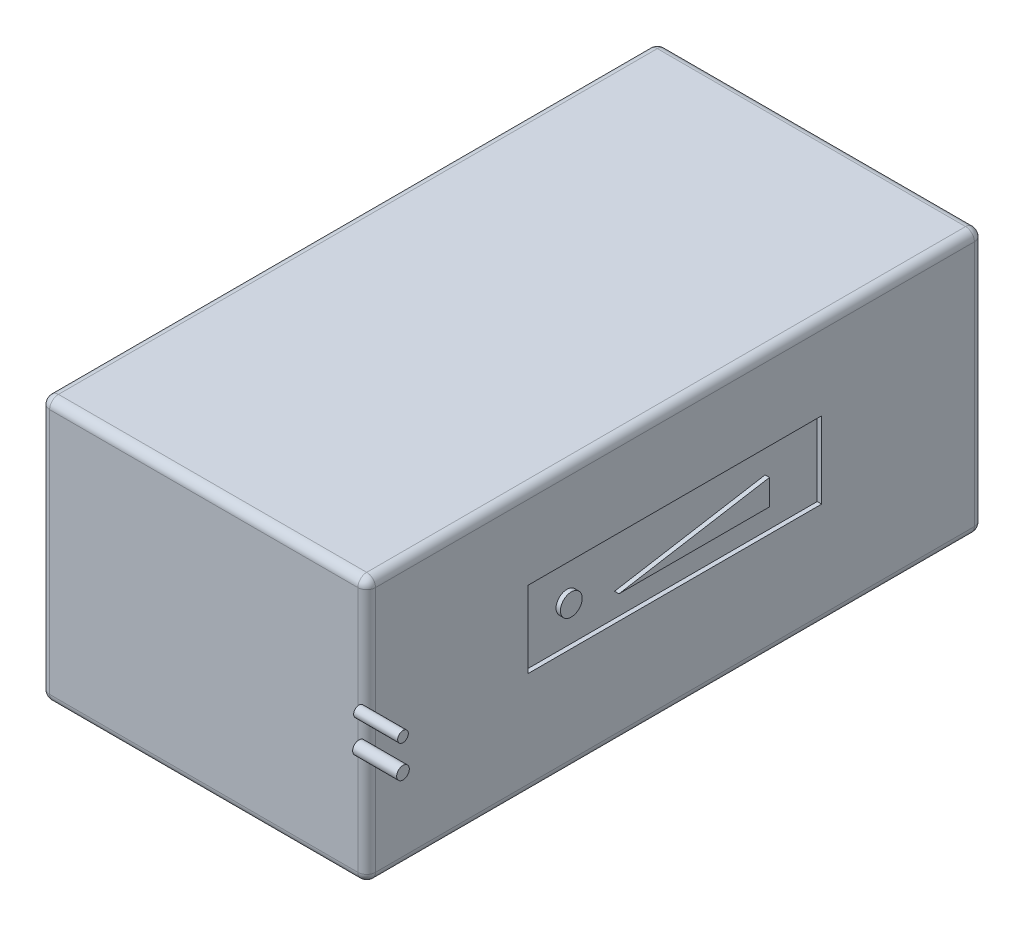
SolidWorks part; units mm, degrees
ref_plane "前视基准面" through (0, 0, 0) normal (0, 0, 1) x (1, 0, 0)
ref_plane "上视基准面" through (0, 0, 0) normal (0, 1, 0) x (1, 0, 0)
ref_plane "右视基准面" through (0, 0, 0) normal (1, 0, 0) x (0, 0, -1)
sketch "草图1" plane through (0, 0, 0) normal (0, 1, 0) x (1, 0, 0)
  line L1 (-37, 70) -> (37, 70)
  line L2 (-37, 70) -> (-37, -70)
  line L3 (-37, -70) -> (37, -70)
  line L4 (37, 70) -> (37, -70)
  line L5 (-37, 70) -> (37, -70) construction
  line L6 (-37, -70) -> (37, 70) construction
  point P0 (0, 0)
  dimension "D1" = 140
  dimension "D2" = 74
extrude "凸台-拉伸1" add sketch "草图1" along normal blind 60
fillet "圆角1" radius 2 12 edges at (-37, 0, 0) (-37, 30, -70) (0, 0, -70) (37, 30, -70) (37, 0, 0) (-37, 30, 70) (37, 30, 70) (0, 0, 70) (0, 60, 70) (-37, 60, 0) (0, 60, -70) (37, 60, 0)
sketch "草图2" plane through (37, 0, 0) normal (1, 0, 0) x (0, 0, -1)
  line L0 (-12.709, 29.1348) -> (21.4754, 29.1348)
  line L1 (-33.3184, 41.1325) -> (33.3184, 41.1325)
  line L2 (-33.3184, 41.1325) -> (-33.3184, 23.7627)
  line L3 (-33.3184, 23.7627) -> (33.3184, 23.7627)
  line L4 (33.3184, 41.1325) -> (33.3184, 23.7627)
  line L5 (-33.3184, 41.1325) -> (33.3184, 23.7627) construction
  line L6 (-33.3184, 23.7627) -> (33.3184, 41.1325) construction
  line L7 (21.4754, 29.1348) -> (21.4754, 34.9192)
  line L8 (21.4754, 34.9192) -> (-12.709, 29.1348)
  circle A0 centre (-23.5282, 32.4476) radius 2.4716
  point P0 (0, 32.4476)
extrude "切除-拉伸1" cut sketch "草图2" against normal blind 1
sketch "草图3" plane through (37, 0, 0) normal (1, 0, 0) x (0, 0, -1)
  circle A0 centre (-71.7557, 35.5772) radius 1.2064
  circle A1 centre (-71.7557, 28.4815) radius 1.4357
extrude "凸台-拉伸2" add sketch "草图3" along normal blind 10
